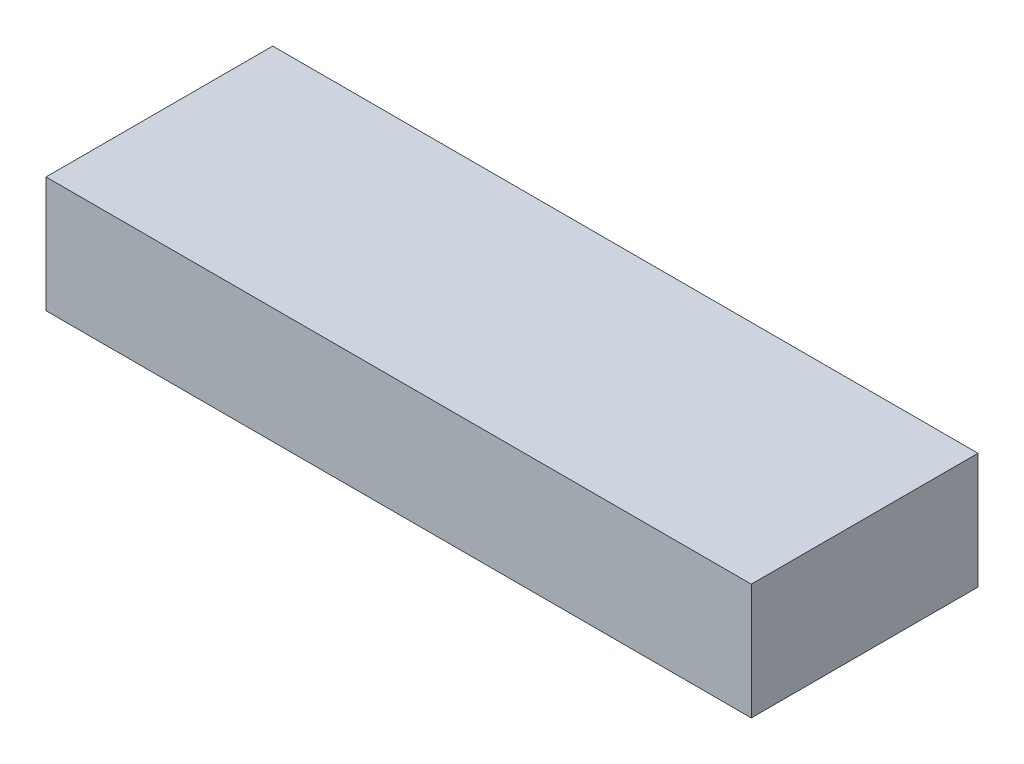
SolidWorks part; units mm, degrees
ref_plane "Front Plane" through (0, 0, 0) normal (0, 0, 1) x (1, 0, 0)
ref_plane "Top Plane" through (0, 0, 0) normal (0, 1, 0) x (1, 0, 0)
ref_plane "Right Plane" through (0, 0, 0) normal (1, 0, 0) x (0, 0, -1)
sketch "Schizzo1" plane through (0, 0, 0) normal (0, 1, 0) x (1, 0, 0)
  line L1 (70, 22.5) -> (-70, 22.5)
  line L2 (70, 22.5) -> (70, -22.5)
  line L3 (70, -22.5) -> (-70, -22.5)
  line L4 (-70, 22.5) -> (-70, -22.5)
  line L5 (70, 22.5) -> (-70, -22.5) construction
  line L6 (70, -22.5) -> (-70, 22.5) construction
  point P0 (0, 0)
  dimension "D1" = 140
  dimension "D2" = 45
extrude "Estrusione-Estrusione1" add sketch "Schizzo1" along normal blind 23
